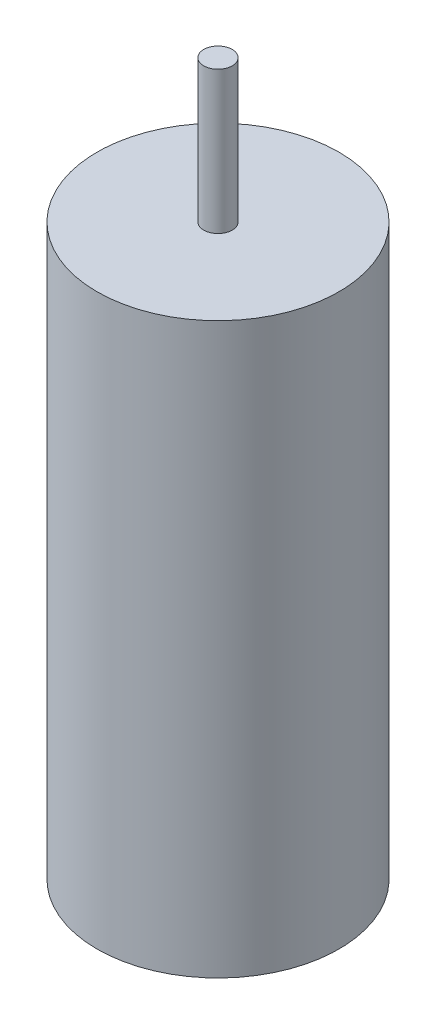
SolidWorks part; units mm, degrees
ref_plane "前视基准面" through (0, 0, 0) normal (0, 0, 1) x (1, 0, 0)
ref_plane "上视基准面" through (0, 0, 0) normal (0, 1, 0) x (1, 0, 0)
ref_plane "右视基准面" through (0, 0, 0) normal (1, 0, 0) x (0, 0, -1)
sketch "草图1" plane through (0, 0, 0) normal (0, 1, 0) x (1, 0, 0)
  circle A0 centre (0, 0) radius 4.25
  dimension "D1" = 8.5
extrude "凸台-拉伸1" add sketch "草图1" along normal blind 20 contours A0
sketch "草图2" plane through (0, 20, 0) normal (0, 1, 0) x (1, 0, 0)
  circle A0 centre (0, 0) radius 0.5
  dimension "D1" = 1
extrude "凸台-拉伸2" add sketch "草图2" along normal blind 5 contours A0
